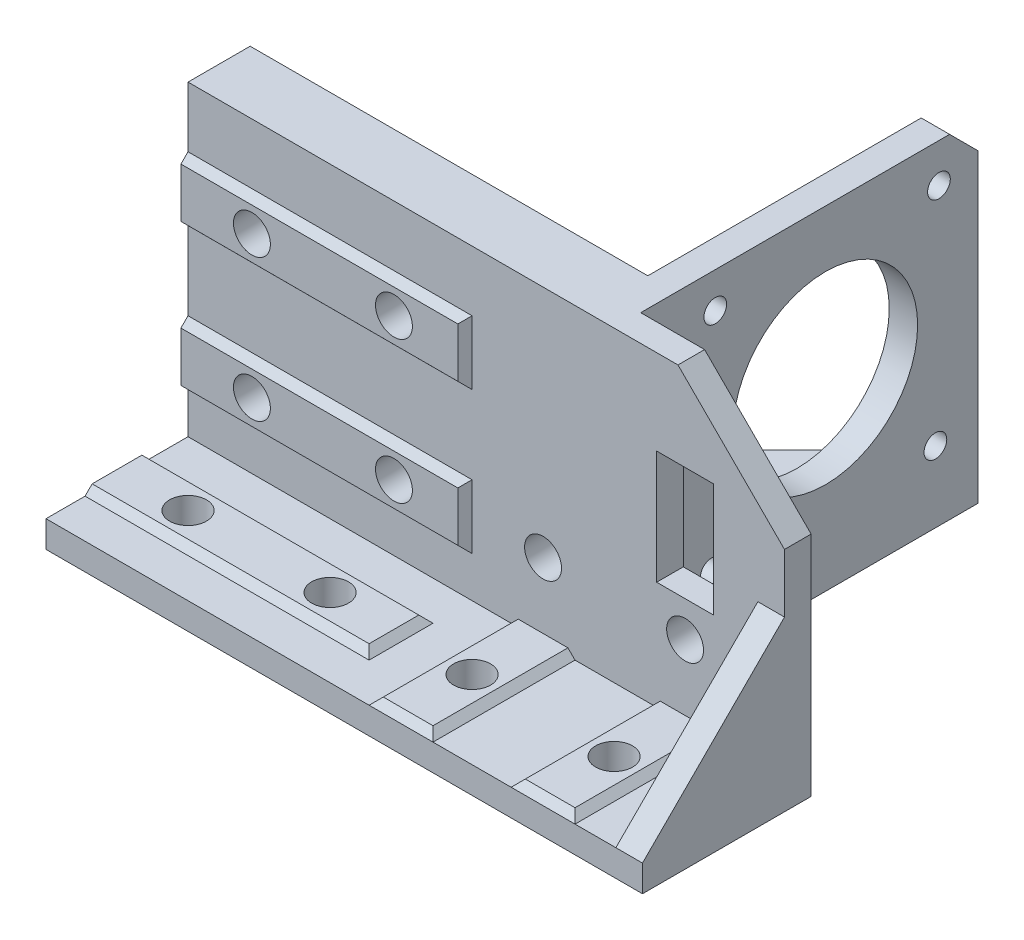
SolidWorks part; units mm, degrees
ref_plane "Front Plane" through (0, 0, 0) normal (0, 0, 1) x (1, 0, 0)
ref_plane "Top Plane" through (0, 0, 0) normal (0, 1, 0) x (1, 0, 0)
ref_plane "Right Plane" through (0, 0, 0) normal (1, 0, 0) x (0, 0, -1)
sketch "Sketch1" plane through (0, 0, 0) normal (0, 0, 1) x (1, 0, 0)
  line L0 (0, 0) -> (0, 47)
  line L1 (0, 0) -> (84, 0)
  line L2 (0, 47) -> (69, 47)
  line L3 (84, 0) -> (84, 32)
  line L4 (69, 47) -> (84, 32)
  dimension "D1" = 84
  dimension "D2" = 32
  dimension "D3" = 135
  dimension "D4" = 69
extrude "Boss-Extrude1" add sketch "Sketch1" along normal blind 8.75
sketch "Sketch3" plane through (0, 0, 8.75) normal (0, 0, 1) x (1, 0, 0)
  line L0 (66, 19) -> (66, 35)
  line L1 (66, 19) -> (74, 19)
  line L2 (66, 35) -> (74, 35)
  line L3 (74, 19) -> (74, 35)
  line L4 (69, 47) -> (0, 47) construction
  line L5 (84, 0) -> (84, 32) construction
  dimension "D1" = 8
  dimension "D2" = 16
  dimension "D3" = 28
  dimension "D4" = 18
extrude "Cut-Extrude1" cut sketch "Sketch3" against normal blind 8.75
sketch "Sketch4" plane through (0, 0, 0) normal (0, -1, 0) x (1, 0, 0)
  line L0 (0, 0) -> (0, 28.75)
  line L1 (0, 28.75) -> (84, 28.75)
  line L2 (84, 28.75) -> (84, 0)
  line L3 (64, 0) -> (64, -50.5)
  line L4 (0, 0) -> (84, 0) construction
  line L5 (64, -50.5) -> (13.5, 0)
  line L6 (13.5, 0) -> (0, 0)
  line L7 (64, 0) -> (84, 0)
  line L8 (0, 0) -> (84, 0)
  line M9 (84, 8.75) -> (0, 8.75)
  dimension "D1" = 20
  dimension "D2" = 45
  dimension "D3" = 13.5
  dimension "D4" = 20
extrude "Boss-Extrude2" add sketch "Sketch4" against normal blind 3.75 contours L2 L1 L0 M9
sketch "Sketch5" plane through (0, 0, 0) normal (0, -1, 0) x (1, 0, 0)
  line L0 (0, 0) -> (84, 0) construction
  line L1 (60, -42.5) -> (56, -42.5)
  line L2 (56, -42.5) -> (13.5, 0)
  line L3 (60, 0) -> (60, -42.5)
  line L7 (13.5, 0) -> (60, 0)
  dimension "D1" = 13.5
  dimension "D2" = 24
  dimension "D3" = 4
  dimension "D4" = 42.5
extrude "Boss-Extrude3" add sketch "Sketch5" against normal blind 4.5
sketch "Sketch6" plane through (60, 0, 0) normal (1, 0, 0) x (0, 0, -1)
  line L0 (0, 0) -> (0, 47)
  line L1 (42.5, 0) -> (42.5, 43)
  line L2 (38.5, 47) -> (0, 47)
  line L3 (0, 0) -> (42.5, 0)
  line L4 (42.5, 43) -> (38.5, 47)
  dimension "D1" = 135
  dimension "D2" = 38.5
extrude "Boss-Extrude5" add sketch "Sketch6" against normal blind 4
sketch "Sketch7" plane through (0, 0, 0) normal (0, 0, -1) x (-1, 0, 0)
  line L0 (-66, 19) -> (-74, 19) construction
  line L1 (-84, 0) -> (-84, 32) construction
  circle A0 centre (-70, 14) radius 2.6
  point P4 (-70, 14)
  dimension "D1" = 5.2
  dimension "D2" = 5
  dimension "D3" = 14
extrude "Cut-Extrude2" cut sketch "Sketch7" against normal blind 14
ref_plane "Plane1" through (84, 32, 0) normal (0, 1, 0) x (1, 0, 0)
sketch "Sketch9" plane through (0, 0, 0) normal (0, 0, -1) x (-1, 0, 0)
  line L0 (-84, 0) -> (-84, 32)
  line L1 (-84, 32) -> (-69, 47)
  line L2 (-69, 47) -> (-60, 47)
  line L3 (-60, 47) -> (-60, 0)
  line L4 (-60, 0) -> (-84, 0)
extrude "Cut-Extrude3" cut sketch "Sketch9" against normal blind 5
sketch "Sketch10" plane through (60, 0, 0) normal (1, 0, 0) x (0, 0, -1)
  line L0 (42.5, 0) -> (-5, 0) construction
  line L1 (-5, 0) -> (-5, 47) construction
  circle A0 centre (21, 26) radius 13
  circle A1 centre (37, 41.5) radius 1.6
  circle A2 centre (36.5, 10) radius 1.6
  circle A3 centre (21, 26) radius 13
  circle A4 centre (5, 10.5) radius 1.6
  circle A5 centre (21, 26) radius 13
  circle A6 centre (5.5, 42) radius 1.6
  circle A7 centre (21, 26) radius 13
  point P20 (21, 26)
  dimension "D1" = 26
  dimension "D2" = 26
  dimension "D3" = 26
  dimension "D4" = 42
  dimension "D5" = 3.2
  dimension "D6" = 41.5
  dimension "D7" = 4
extrude "Cut-Extrude4" cut sketch "Sketch10" against normal blind 5 contours A6 | A0 | A1 | A2 | A4
sketch "Sketch11" plane through (0, 0, 0) normal (0, 0, -1) x (-1, 0, 0)
  line L0 (0, 47) -> (0, 0) construction
  line L1 (0, 0) -> (-13.5, 0) construction
  circle A1 centre (-50, 14) radius 4.5
  circle A2 centre (-30, 14) radius 4.5
  circle A3 centre (-10, 14) radius 4.5
  circle A4 centre (-10, 34) radius 4.5
  circle A5 centre (-30, 34) radius 4.5
  point P14 (-6.75, 0)
  dimension "D1" = 10
  dimension "D2" = 20
  dimension "D3" = 14
  dimension "D4" = 20
  dimension "D5" = 20
  dimension "D6" = 9
  dimension "D7" = 9
  dimension "D8" = 9
  dimension "D9" = 9
  dimension "D10" = 9
extrude "Cut-Extrude5" cut sketch "Sketch11" against normal blind 5
sketch "Sketch12" plane through (0, 0, 5) normal (0, 0, -1) x (-1, 0, 0)
  circle A0 centre (-30, 34) radius 2.6
  circle A1 centre (-10, 34) radius 2.6
  circle A2 centre (-10, 14) radius 2.6
  circle A3 centre (-30, 14) radius 2.6
  circle A4 centre (-50, 14) radius 2.6
  dimension "D1" = 5.2
  dimension "D2" = 5.2
  dimension "D3" = 5.2
  dimension "D4" = 5.2
  dimension "D5" = 5.2
extrude "Cut-Extrude6" cut sketch "Sketch12" against normal blind 3.75
sketch "Sketch13" plane through (0, 0, 8.75) normal (0, 0, 1) x (1, 0, 0)
  line L0 (0, 38.5) -> (40, 38.5)
  line L1 (0, 38.5) -> (0, 29.5)
  line L2 (40, 38.5) -> (40, 29.5)
  line L3 (0, 29.5) -> (40, 29.5)
  line L4 (0, 47) -> (0, 3.75) construction
  line L5 (0, 18.5) -> (40, 18.5)
  line L6 (0, 18.5) -> (0, 9.5)
  line L7 (40, 18.5) -> (40, 9.5)
  line L8 (0, 9.5) -> (40, 9.5)
  line L9 (0, 0) -> (84, 0) construction
  dimension "D1" = 9
  dimension "D2" = 9
  dimension "D3" = 40
  dimension "D4" = 20
  dimension "D5" = 9.5
extrude "Boss-Extrude6" add sketch "Sketch13" along normal blind 1
sketch "Sketch14" plane through (0, 0, 0) normal (-1, 0, 0) x (0, 0, 1)
  line L0 (8.75, 38.5) -> (9.75, 37.5)
  line L1 (9.75, 38.5) -> (9.75, 29.5) construction
  line L2 (9.75, 37.5) -> (9.75, 38.5)
  line L3 (9.75, 38.5) -> (8.75, 38.5)
  line L4 (9.75, 29.5) -> (9.75, 30.5027)
  line L5 (9.75, 30.5027) -> (8.75, 29.5)
  line L6 (9.75, 18.5) -> (8.75, 18.5)
  line L7 (8.75, 18.5) -> (9.75, 17.5)
  line L8 (9.75, 18.5) -> (9.75, 9.5) construction
  line L9 (9.75, 17.5) -> (9.75, 18.5)
  line L10 (9.75, 9.5) -> (9.75, 10.5)
  line L11 (9.75, 10.5) -> (8.75, 9.5)
  line L13 (9.75, 29.5) -> (8.75, 29.5)
  line L14 (9.75, 9.5) -> (8.75, 9.5)
  dimension "D1" = 1
  dimension "D2" = 1
  dimension "D3" = 1.0027
  dimension "D4" = 1
sketch "Sketch16" plane through (0, 38.5, 0) normal (0, 1, 0) x (1, 0, 0)
  line L0 (40, -8.75) -> (39, -9.75)
  line L1 (40, -9.75) -> (0, -9.75) construction
  line L2 (39, -9.75) -> (40, -9.75)
  line L3 (40, -9.75) -> (40, -8.75)
  dimension "D1" = 1
extrude "Cut-Extrude14" cut sketch "Sketch16" against normal blind 31
extrude "Cut-Extrude15" cut sketch "Sketch14" against normal blind 42
sketch "Sketch17" plane through (0, 3.75, 0) normal (0, 1, 0) x (1, 0, 0)
  line L0 (0, -14.25) -> (40, -14.25)
  line L1 (0, -14.25) -> (0, -23.25)
  line L2 (40, -14.25) -> (40, -23.25)
  line L3 (0, -23.25) -> (40, -23.25)
  line L4 (0, -8.75) -> (0, -28.75) construction
  line L5 (0, -28.75) -> (84, -28.75) construction
  dimension "D1" = 9
  dimension "D2" = 5.5
  dimension "D3" = 40
extrude "Boss-Extrude7" add sketch "Sketch17" along normal blind 1
sketch "Sketch18" plane through (0, 0, 23.25) normal (0, 0, 1) x (1, 0, 0)
  line L0 (40, 4.75) -> (39, 4.75)
  line L1 (0, 4.75) -> (40, 4.75) construction
  line L2 (39, 4.75) -> (40, 3.75)
  line L3 (40, 3.75) -> (40, 4.75)
  dimension "D1" = 1
extrude "Cut-Extrude16" cut sketch "Sketch18" against normal blind 10
sketch "Sketch19" plane through (0, 0, 0) normal (-1, 0, 0) x (0, 0, 1)
  line L0 (14.25, 4.75) -> (14.25, 3.75)
  line L1 (14.25, 3.75) -> (15.25, 4.75)
  line L2 (14.25, 4.75) -> (23.25, 4.75) construction
  line L3 (15.25, 4.75) -> (14.25, 4.75)
  line L4 (23.25, 4.75) -> (23.25, 3.75)
  line L5 (23.25, 4.75) -> (23.25, 3.75) construction
  line L6 (23.25, 3.75) -> (22.25, 4.75)
  line L7 (22.25, 4.75) -> (23.25, 4.75)
  dimension "D1" = 1
  dimension "D2" = 1
extrude "Cut-Extrude17" cut sketch "Sketch19" against normal blind 40
sketch "Sketch20" plane through (0, 3.75, 0) normal (0, 1, 0) x (1, 0, 0)
  line L0 (45.5, -8.75) -> (45.5, -28.75)
  line L1 (45.5, -8.75) -> (54.5, -8.75)
  line L2 (45.5, -28.75) -> (54.5, -28.75)
  line L3 (54.5, -8.75) -> (54.5, -28.75)
  line L4 (84, -8.75) -> (0, -8.75) construction
  line L5 (0, -28.75) -> (84, -28.75) construction
  line L6 (65.5, -8.75) -> (65.5, -28.75)
  line L7 (65.5, -8.75) -> (74.5, -8.75)
  line L8 (65.5, -28.75) -> (74.5, -28.75)
  line L9 (74.5, -8.75) -> (74.5, -28.75)
  line L10 (84, -28.75) -> (84, -8.75) construction
  dimension "D1" = 9
  dimension "D2" = 9
  dimension "D3" = 11
  dimension "D4" = 9.5
extrude "Boss-Extrude8" add sketch "Sketch20" along normal blind 1
sketch "Sketch21" plane through (45.5, 0, 0) normal (-1, 0, 0) x (0, 0, 1)
  line L0 (28.75, 3.75) -> (28.75, 4.75)
  line L1 (28.75, 4.75) -> (27.75, 4.75)
  line L2 (8.75, 4.75) -> (28.75, 4.75) construction
  line L3 (27.75, 4.75) -> (28.75, 3.75)
  dimension "D1" = 1
sketch "Sketch22" plane through (0, 0, 28.75) normal (0, 0, 1) x (1, 0, 0)
  line L0 (45.5, 3.75) -> (45.5, 4.75)
  line L1 (45.5, 4.75) -> (54.5, 4.75) construction
  line L2 (45.5, 4.75) -> (45.5, 3.75) construction
  line L3 (45.5, 4.75) -> (46.5, 4.75)
  line L4 (46.5, 4.75) -> (45.5, 3.75)
  line L5 (54.5, 4.75) -> (54.5, 3.75)
  line L6 (54.5, 3.75) -> (53.5, 4.75)
  line L7 (53.5, 4.75) -> (54.5, 4.75)
  line L8 (65.5, 4.75) -> (66.5, 4.75)
  line L9 (65.5, 4.75) -> (74.5, 4.75) construction
  line L10 (66.5, 4.75) -> (65.5, 3.75)
  line L11 (65.5, 3.75) -> (65.5, 4.75)
  line L12 (74.5, 4.75) -> (74.5, 3.75)
  line L13 (74.5, 3.75) -> (73.5, 4.75)
  line L14 (73.5, 4.75) -> (74.5, 4.75)
  dimension "D1" = 1
  dimension "D2" = 1
  dimension "D3" = 1
  dimension "D4" = 1
extrude "Cut-Extrude19" cut sketch "Sketch22" against normal blind 20
extrude "Cut-Extrude20" cut sketch "Sketch21" against normal blind 30
sketch "Sketch23" plane through (0, 0, 8.75) normal (0, 0, -1) x (-1, 0, 0)
  circle A0 centre (-30, 34) radius 2.6
  circle A1 centre (-10, 34) radius 2.6
  circle A2 centre (-30, 14) radius 2.6
  circle A3 centre (-10, 14) radius 2.6
extrude "Cut-Extrude21" cut sketch "Sketch23" against normal blind 1
sketch "Sketch24" plane through (0, 4.75, 0) normal (0, 1, 0) x (1, 0, 0)
  line L0 (53.5, -8.75) -> (53.5, -27.75) construction
  line L1 (54.5, -28.75) -> (45.5, -28.75) construction
  line L2 (66.5, -8.75) -> (66.5, -27.75) construction
  line L3 (39, -22.25) -> (0, -22.25) construction
  line L4 (0, -15.25) -> (0, -22.25) construction
  circle A0 centre (10, -18.75) radius 2.6
  circle A1 centre (30, -18.75) radius 2.6
  circle A2 centre (50, -18.75) radius 2.6
  circle A3 centre (70, -18.75) radius 2.6
  point P13 (70.5673, -16.8085)
  dimension "D1" = 5.2
  dimension "D2" = 5.2
  dimension "D3" = 5.2
  dimension "D4" = 5.2
  dimension "D6" = 3.5
  dimension "D5" = 10
  dimension "D7" = 3.5
  dimension "D8" = 3.5
  dimension "D9" = 10
  dimension "D10" = 20
extrude "Cut-Extrude22" cut sketch "Sketch24" against normal blind 12
sketch "Sketch25" plane through (84, 0, 0) normal (1, 0, 0) x (0, 0, -1)
  line L0 (-8.75, 23.75) -> (-28.75, 3.75)
  line L1 (-8.75, 3.75) -> (-8.75, 32) construction
  line L2 (-28.75, 3.75) -> (-8.75, 3.75) construction
  line L3 (-28.75, 3.75) -> (-8.75, 3.75)
  line L4 (-8.75, 3.75) -> (-8.75, 23.75)
  point P6 (-27.5568, 3.75)
  dimension "D1" = 135
extrude "Boss-Extrude9" add sketch "Sketch25" against normal blind 3.75
